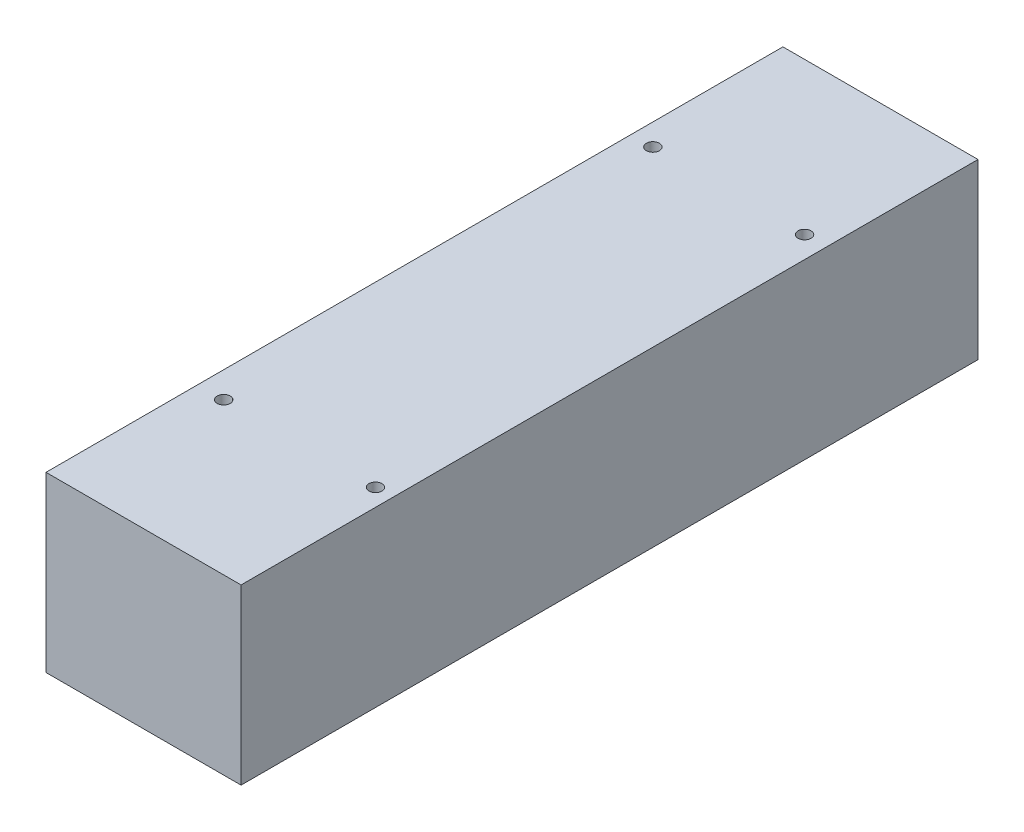
SolidWorks part; units mm, degrees
ref_plane "Plan de face" through (0, 0, 0) normal (0, 0, 1) x (1, 0, 0)
ref_plane "Plan de dessus" through (0, 0, 0) normal (0, 1, 0) x (1, 0, 0)
ref_plane "Plan de droite" through (0, 0, 0) normal (1, 0, 0) x (0, 0, -1)
sketch "Esquisse1" plane through (0, 0, 0) normal (0, 0, 1) x (1, 0, 0)
  line L1 (-36.1156, 22.4038) -> (8.8844, 22.4038)
  line L2 (-36.1156, 22.4038) -> (-36.1156, -17.5962)
  line L3 (-36.1156, -17.5962) -> (8.8844, -17.5962)
  line L4 (8.8844, 22.4038) -> (8.8844, -17.5962)
  dimension "D1" = 40
  dimension "D2" = 45
extrude "Boss.-Extru.1" add sketch "Esquisse1" along normal blind 170
sketch "Esquisse2" plane through (0, 22.4038, 0) normal (0, 1, 0) x (1, 0, 0)
  line L0 (-36.1156, -170) -> (-36.1156, 0) construction
  line L1 (8.8844, -170) -> (-36.1156, -170) construction
  circle A0 centre (-31.1156, -35.005) radius 1.5
  circle A1 centre (3.8844, -35.005) radius 1.5
  circle A2 centre (-30.1156, -135) radius 1.5
  circle A3 centre (4.8844, -135) radius 1.5
  point P12 (6.3844, -129.0783)
  point P13 (34.629, -116.9352)
  dimension "D1" = 35
  dimension "D2" = 3
  dimension "D3" = 3
  dimension "D6" = 3
  dimension "D8" = 3
  dimension "D11" = 35
  dimension "D4" = 5
  dimension "D5" = 6
  dimension "D7" = 100
  dimension "D9" = 35
  dimension "D10" = 100
extrude "Enlèv. mat.-Extru.1" cut sketch "Esquisse2" against normal blind 6
